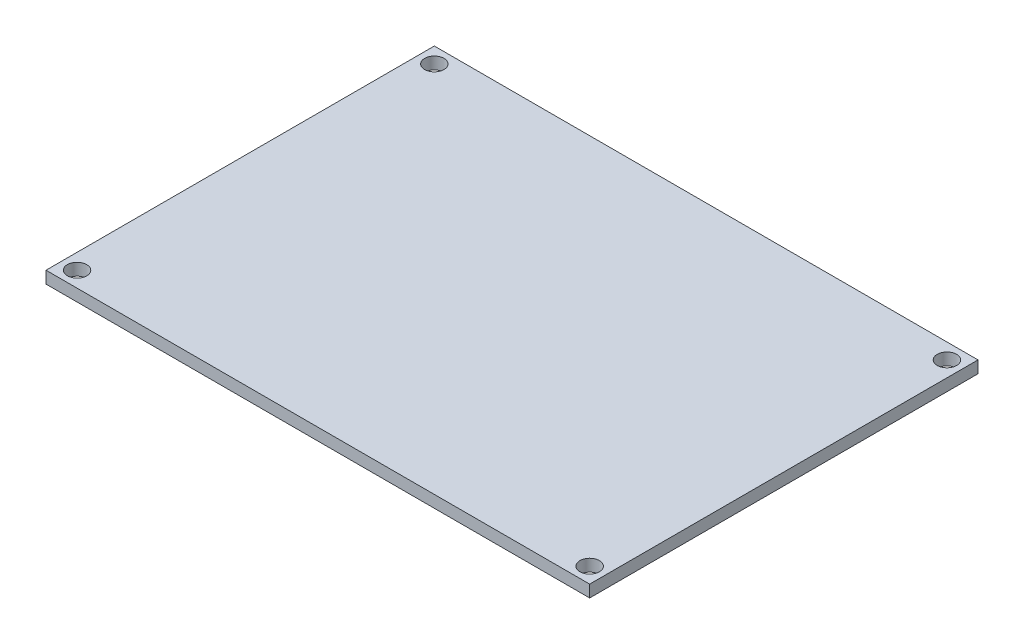
SolidWorks part; units mm, degrees
ref_plane "Front Plane" through (0, 0, 0) normal (0, 0, 1) x (1, 0, 0)
ref_plane "Top Plane" through (0, 0, 0) normal (0, 1, 0) x (1, 0, 0)
ref_plane "Right Plane" through (0, 0, 0) normal (1, 0, 0) x (0, 0, -1)
sketch "Sketch1" plane through (0, 0, 0) normal (0, 1, 0) x (1, 0, 0)
  line L1 (0, 0) -> (70, 0)
  line L2 (0, 0) -> (0, 50)
  line L3 (0, 50) -> (70, 50)
  line L4 (70, 0) -> (70, 50)
  dimension "D1" = 70
  dimension "D2" = 50
extrude "Boss-Extrude1" add sketch "Sketch1" along normal blind 1.55
sketch "Sketch2" plane through (0, 1.55, 0) normal (0, 1, 0) x (1, 0, 0)
  line L0 (70, 50) -> (0, 50) construction
  line L1 (2, 48) -> (68, 48) construction
  line L2 (2, 48) -> (2, 2) construction
  line L3 (2, 2) -> (68, 2) construction
  line L4 (68, 48) -> (68, 2) construction
  line L5 (0, 50) -> (0, 0) construction
  line L6 (70, 0) -> (70, 50) construction
  line L7 (0, 0) -> (70, 0) construction
  circle A0 centre (2, 48) radius 1.25
  circle A1 centre (68, 48) radius 1.25
  circle A2 centre (68, 2) radius 1.25
  circle A3 centre (2, 2) radius 1.25
  dimension "D5" = 2.5
  dimension "D6" = 2.5
  dimension "D7" = 2.5
  dimension "D8" = 2.5
  dimension "D1" = 2
  dimension "D2" = 2
  dimension "D3" = 2
  dimension "D4" = 2
extrude "Cut-Extrude1" cut sketch "Sketch2" against normal through all
